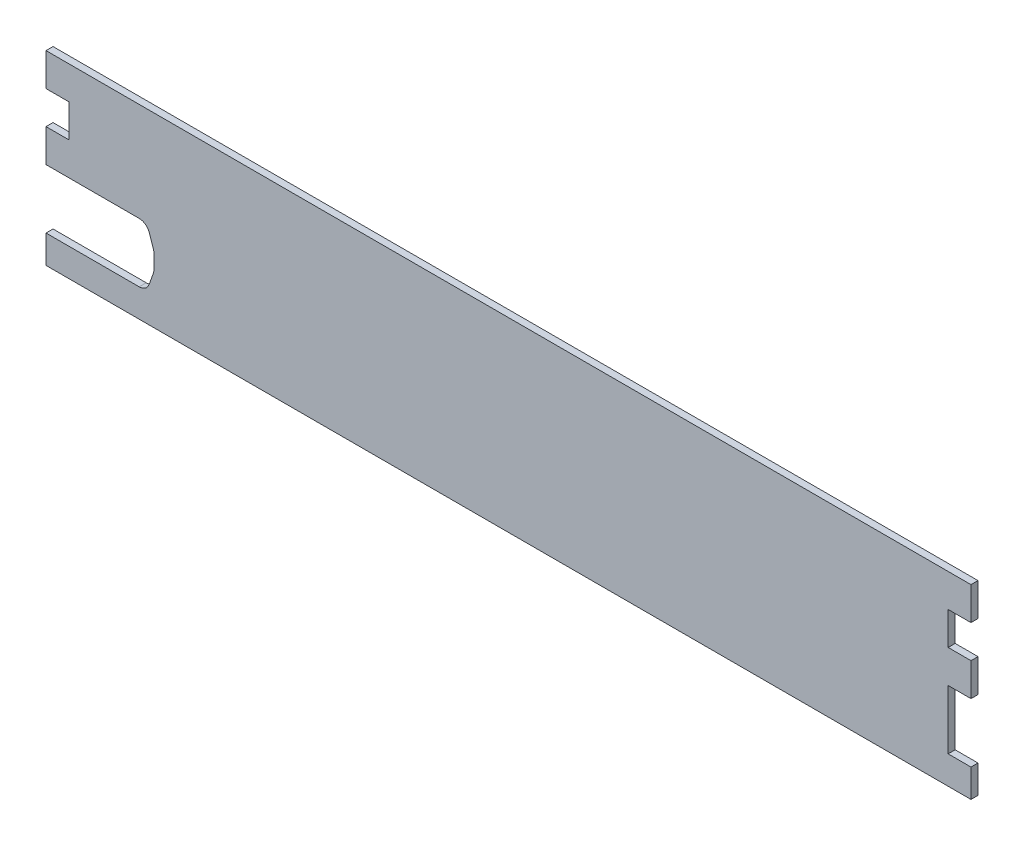
SolidWorks part; units mm, degrees
ref_plane "Face" through (0, 0, 0) normal (0, 0, 1) x (1, 0, 0)
ref_plane "Dessus" through (0, 0, 0) normal (0, 1, 0) x (1, 0, 0)
ref_plane "Droite" through (0, 0, 0) normal (1, 0, 0) x (0, 0, -1)
sketch "Esquisse1" plane through (0, 0, 0) normal (0, 0, 1) x (1, 0, 0)
  line L0 (-878.2483, 39.9967) -> (-878.2483, -91.9002) construction
  line L1 (-878.2483, 39.9967) -> (-878.2483, -91.9002) construction
  line L2 (-875.7483, -75.1858) -> (-878.2483, -75.1858)
  line L3 (-875.7483, -67.1858) -> (-878.2483, -67.1858)
  line L4 (-875.7483, -50.3128) -> (-878.2483, -50.3128)
  line L5 (-875.7483, -40.9357) -> (-878.2483, -40.9357)
  line L6 (-875.7483, -31.5585) -> (-878.2483, -31.5585)
  line L7 (-875.7483, -22.1814) -> (-878.2483, -22.1814)
  line L8 (-746.4983, -22.1814) -> (-746.4983, -75.1858) construction
  line L9 (-614.7483, 39.9967) -> (-614.7483, -31.5585) construction
  line L10 (-617.2483, -75.1858) -> (-614.7483, -75.1858)
  line L11 (-617.2483, -67.1858) -> (-614.7483, -67.1858)
  line L13 (-617.2483, -40.9357) -> (-614.7483, -40.9357)
  line L14 (-617.2483, -31.5585) -> (-614.7483, -31.5585)
  line L15 (-617.2483, -22.1814) -> (-614.7483, -22.1814)
  line L16 (-614.7483, -40.9357) -> (-614.7483, -50.3128)
  line L17 (-614.7483, -67.1858) -> (-614.7483, -91.9002) construction
  line L18 (-614.7483, -75.1858) -> (-614.7483, -67.1858)
  line L19 (-614.7483, -31.5585) -> (-614.7483, -22.1814)
  line L20 (-878.2483, -75.1858) -> (-878.2483, -67.1858)
  line L21 (-878.2483, -50.3128) -> (-878.2483, -40.9357)
  line L22 (-617.2483, -67.1858) -> (-621.2483, -67.1858)
  line L23 (-621.2483, -67.1858) -> (-621.2483, -50.3128)
  line L24 (-621.2483, -50.3128) -> (-617.2483, -50.3128)
  line L25 (-617.2483, -50.3128) -> (-617.2483, -40.9357)
  line L26 (-617.2483, -40.9357) -> (-621.2483, -40.9357)
  line L27 (-621.2483, -40.9357) -> (-621.2483, -31.5585)
  line L28 (-621.2483, -31.5585) -> (-617.2483, -31.5585)
  line L29 (-617.2483, -31.5585) -> (-617.2483, -22.1814)
  line L30 (-617.2483, -22.1814) -> (-875.7483, -22.1814)
  line L31 (-875.7483, -22.1814) -> (-875.7483, -31.5585)
  line L32 (-875.7483, -31.5585) -> (-871.7483, -31.5585)
  line L33 (-871.7483, -31.5585) -> (-871.7483, -40.9357)
  line L34 (-871.7483, -40.9357) -> (-875.7483, -40.9357)
  line L35 (-875.7483, -40.9357) -> (-875.7483, -50.3128)
  line L36 (-875.7483, -50.3128) -> (-851.6983, -50.3128)
  line L37 (-848.8592, -52.3435) -> (-847.6592, -55.8585)
  line L38 (-847.4983, -56.8278) -> (-847.4983, -60.8278)
  line L39 (-847.6733, -61.8373) -> (-848.8733, -65.1953)
  line L40 (-851.6983, -67.1858) -> (-875.7483, -67.1858)
  line L41 (-875.7483, -67.1858) -> (-875.7483, -75.1858)
  line L42 (-875.7483, -75.1858) -> (-617.2483, -75.1858)
  line L43 (-617.2483, -75.1858) -> (-617.2483, -67.1858)
  line L44 (-617.2483, -67.1858) -> (-621.2483, -67.1858)
  line L47 (-617.2483, -50.3128) -> (-617.2483, -40.9357) construction
  line L48 (-617.2483, -40.9357) -> (-621.2483, -40.9357)
  line L49 (-621.2483, -40.9357) -> (-621.2483, -31.5585)
  line L50 (-621.2483, -31.5585) -> (-617.2483, -31.5585)
  line L51 (-617.2483, -31.5585) -> (-617.2483, -22.1814) construction
  line L52 (-617.2483, -22.1814) -> (-875.7483, -22.1814)
  line L53 (-875.7483, -22.1814) -> (-875.7483, -31.5585) construction
  line L54 (-875.7483, -31.5585) -> (-871.7483, -31.5585)
  line L55 (-871.7483, -31.5585) -> (-871.7483, -40.9357)
  line L56 (-871.7483, -40.9357) -> (-875.7483, -40.9357)
  line L57 (-875.7483, -40.9357) -> (-875.7483, -50.3128) construction
  line L58 (-875.7483, -50.3128) -> (-851.6983, -50.3128)
  line L59 (-848.8592, -52.3435) -> (-847.6592, -55.8585)
  line L60 (-847.4983, -56.8278) -> (-847.4983, -60.8278)
  line L61 (-847.6733, -61.8373) -> (-848.8733, -65.1953)
  line L62 (-851.6983, -67.1858) -> (-875.7483, -67.1858)
  line L63 (-875.7483, -67.1858) -> (-875.7483, -75.1858) construction
  line L64 (-875.7483, -75.1858) -> (-617.2483, -75.1858)
  line L65 (-617.2483, -75.1858) -> (-617.2483, -67.1858) construction
  line L66 (-878.2483, -31.5585) -> (-878.2483, -22.1814)
  line L67 (-614.7483, -50.3128) -> (-621.2483, -50.3128)
  line L68 (-621.2483, -50.3128) -> (-621.2483, -67.1858)
  arc A4 (-848.8592, -52.3435) -> (-851.6983, -50.3128) centre (-851.6983, -53.3128) ccw
  arc A5 (-847.4983, -56.8278) -> (-847.6592, -55.8585) centre (-850.4983, -56.8278) ccw
  arc A6 (-847.6733, -61.8373) -> (-847.4983, -60.8278) centre (-850.4983, -60.8278) ccw
  arc A7 (-851.6983, -67.1858) -> (-848.8733, -65.1953) centre (-851.6983, -64.1858) ccw
  arc A8 (-848.8592, -52.3435) -> (-851.6983, -50.3128) centre (-851.6983, -53.3128) ccw
  arc A9 (-847.4983, -56.8278) -> (-847.6592, -55.8585) centre (-850.4983, -56.8278) ccw
  arc A10 (-847.6733, -61.8373) -> (-847.4983, -60.8278) centre (-850.4983, -60.8278) ccw
  arc A11 (-851.6983, -67.1858) -> (-848.8733, -65.1953) centre (-851.6983, -64.1858) ccw
  dimension "D1" = 0
extrude "Boss.-Extru.1" add sketch "Esquisse1" against normal blind 2
